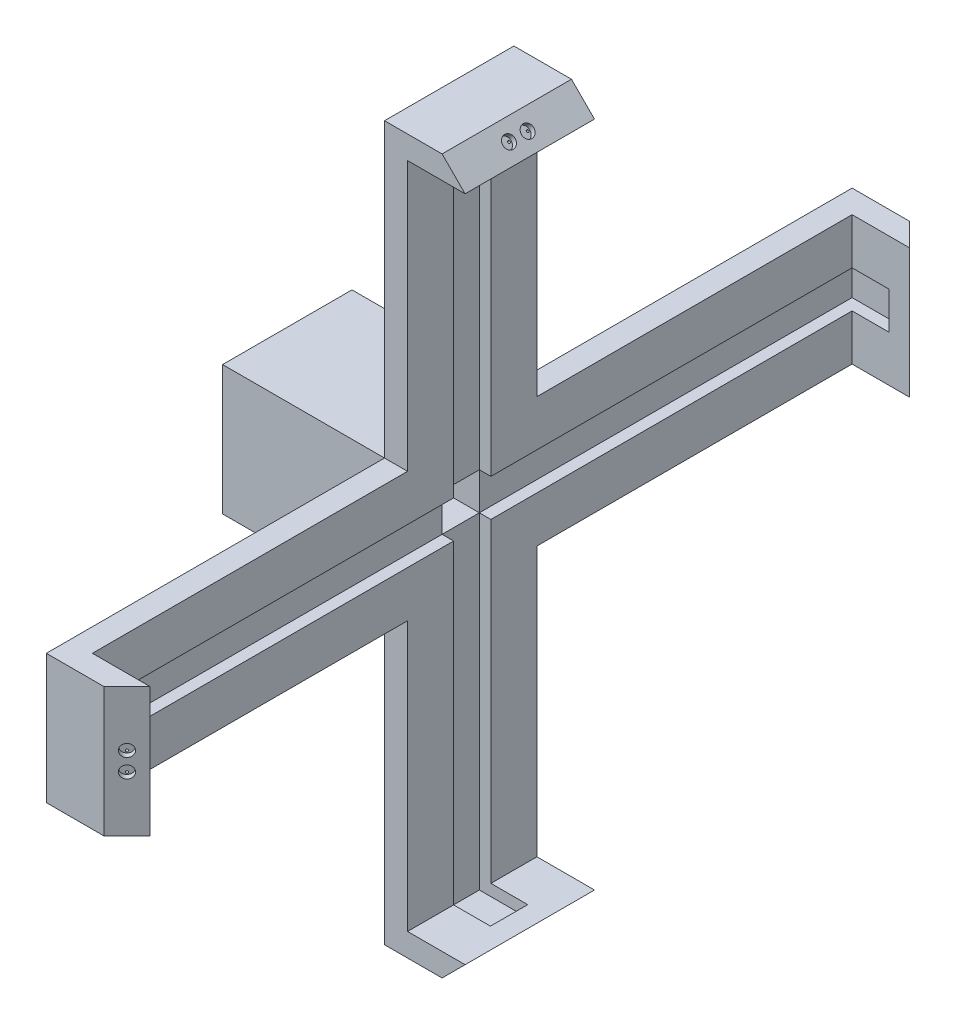
SolidWorks part; units mm, degrees
ref_plane "Front Plane" through (0, 0, 0) normal (0, 0, 1) x (1, 0, 0)
ref_plane "Top Plane" through (0, 0, 0) normal (0, 1, 0) x (1, 0, 0)
ref_plane "Right Plane" through (0, 0, 0) normal (1, 0, 0) x (0, 0, -1)
sketch "Sketch1" plane through (0, 0, 0) normal (0, 0, 1) x (1, 0, 0)
  circle A0 centre (0, 0) radius 28.1
extrude "Boss-Extrude2" add sketch "Sketch1" along normal blind 24
sketch "Sketch3" plane through (0, 0, 0) normal (0, 0, -1) x (-1, 0, 0)
  line L2 (-1.6618, 2.5) -> (1.6618, 2.5)
  arc A1 (-1.6618, 2.5) -> (1.6618, 2.5) centre (0, 0) ccw
extrude "Cut-Extrude2" cut sketch "Sketch3" against normal blind 21.5
sketch "Sketch4" plane through (0, 0, 0) normal (0, 0, -1) x (-1, 0, 0)
  circle A0 centre (0, 0) radius 3
extrude "Cut-Extrude3" cut sketch "Sketch4" against normal blind 9.5
sketch "Sketch6" plane through (0, 0, 0) normal (0, 0, -1) x (-1, 0, 0)
  circle A0 centre (0, 0) radius 6.025
extrude "Cut-Extrude4" cut sketch "Sketch6" against normal blind 6.2
sketch "Sketch7" plane through (0, 0, 24) normal (0, 0, 1) x (1, 0, 0)
  line L1 (-28.1, -28.1) -> (28.1, -28.1)
  line L2 (-28.1, -28.1) -> (-28.1, 28.1)
  line L3 (-28.1, 28.1) -> (28.1, 28.1)
  line L4 (28.1, -28.1) -> (28.1, 28.1)
  line L5 (-28.1, -28.1) -> (28.1, 28.1) construction
  line L6 (-28.1, 28.1) -> (28.1, -28.1) construction
  point P0 (0, 0)
extrude "Boss-Extrude3" add sketch "Sketch7" along normal blind 56.2
sketch "Sketch8" plane through (28.1, 0, 0) normal (1, 0, 0) x (0, 0, -1)
  line L0 (-80.2, 28.1) -> (-24, 28.1) construction
  line L1 (-80.2, 28.1) -> (-24, 28.1)
  line L2 (-80.2, 28.1) -> (-80.2, -28.1)
  line L3 (-80.2, -28.1) -> (-24, -28.1)
  line L4 (-24, 28.1) -> (-24, -28.1)
  line L5 (-80.2, -28.1) -> (-80.2, 28.1) construction
extrude "Boss-Extrude4" add sketch "Sketch8" along normal blind 14.14
sketch "Sketch10" plane through (42.24, 0, 0) normal (1, 0, 0) x (0, 0, -1)
  line L1 (-80.2, 28.1) -> (-24, 28.1)
  line L2 (-80.2, 28.1) -> (-80.2, -28.1)
  line L3 (-80.2, -28.1) -> (-24, -28.1)
  line L4 (-24, 28.1) -> (-24, -28.1)
extrude "Boss-Extrude5" add sketch "Sketch10" along normal blind 10
sketch "Sketch11" plane through (0, 0, 80.2) normal (0, 0, 1) x (1, 0, 0)
  line L1 (52.24, 28.1) -> (-28.1, 28.1) construction
  line L3 (42.24, 28.1) -> (52.24, 28.1)
  line L4 (42.24, 28.1) -> (42.24, -28.1)
  line L5 (42.24, -28.1) -> (52.24, -28.1)
  line L6 (52.24, 28.1) -> (52.24, -28.1)
extrude "Boss-Extrude6" add sketch "Sketch11" along normal blind 146.9
sketch "Sketch12" plane through (0, 28.1, 0) normal (0, 1, 0) x (1, 0, 0)
  line L1 (42.24, -80.2) -> (52.24, -80.2)
  line L2 (42.24, -80.2) -> (42.24, -24)
  line L3 (42.24, -24) -> (52.24, -24)
  line L4 (52.24, -80.2) -> (52.24, -24)
extrude "Boss-Extrude7" add sketch "Sketch12" along normal blind 126.9
sketch "Sketch13" plane through (0, 0, 24) normal (0, 0, -1) x (-1, 0, 0)
  line L1 (-52.24, -28.1) -> (-42.24, -28.1)
  line L2 (-52.24, -28.1) -> (-52.24, 28.1)
  line L3 (-52.24, 28.1) -> (-42.24, 28.1)
  line L4 (-42.24, -28.1) -> (-42.24, 28.1)
extrude "Boss-Extrude8" add sketch "Sketch13" along normal blind 146.9
sketch "Sketch14" plane through (0, -28.1, 0) normal (0, -1, 0) x (-1, 0, 0)
  line L0 (-52.24, -227.1) -> (-52.24, 122.9) construction
  line L1 (-42.24, -24) -> (-52.24, -24)
  line L2 (-42.24, -24) -> (-42.24, -80.2)
  line L3 (-42.24, -80.2) -> (-52.24, -80.2)
  line L4 (-52.24, -24) -> (-52.24, -80.2)
extrude "Boss-Extrude9" add sketch "Sketch14" along normal blind 126.9
sketch "Sketch15" plane through (52.24, 0, 0) normal (1, 0, 0) x (0, 0, -1)
  line L1 (-80.2, 28.1) -> (-227.1, 28.1) construction
  line L3 (-217.1, 28.1) -> (-227.1, 28.1)
  line L4 (-217.1, 28.1) -> (-217.1, -28.1)
  line L5 (-217.1, -28.1) -> (-227.1, -28.1)
  line L6 (-227.1, 28.1) -> (-227.1, -28.1)
extrude "Boss-Extrude10" add sketch "Sketch15" along normal blind 25
sketch "Sketch16" plane through (52.24, 0, 0) normal (1, 0, 0) x (0, 0, -1)
  line L1 (122.9, 28.1) -> (-24, 28.1) construction
  line L3 (112.9, 28.1) -> (122.9, 28.1)
  line L4 (112.9, 28.1) -> (112.9, -28.1)
  line L5 (112.9, -28.1) -> (122.9, -28.1)
  line L6 (122.9, 28.1) -> (122.9, -28.1)
extrude "Boss-Extrude11" add sketch "Sketch16" along normal blind 25
sketch "Sketch17" plane through (52.24, 0, 0) normal (1, 0, 0) x (0, 0, -1)
  line L1 (-80.2, 155) -> (-80.2, 28.1) construction
  line L3 (-80.2, 145) -> (-24, 145)
  line L4 (-80.2, 145) -> (-80.2, 155)
  line L5 (-80.2, 155) -> (-24, 155)
  line L6 (-24, 145) -> (-24, 155)
extrude "Boss-Extrude12" add sketch "Sketch17" along normal blind 25
sketch "Sketch18" plane through (52.24, 0, 0) normal (1, 0, 0) x (0, 0, -1)
  line L1 (-80.2, -155) -> (-80.2, -28.1) construction
  line L3 (-80.2, -145) -> (-24, -145)
  line L4 (-80.2, -145) -> (-80.2, -155)
  line L5 (-80.2, -155) -> (-24, -155)
  line L6 (-24, -145) -> (-24, -155)
extrude "Boss-Extrude13" add sketch "Sketch18" along normal blind 25
sketch "Sketch19" plane through (-28.1, 0, 0) normal (-1, 0, 0) x (0, 0, 1)
  line L7 (26.5, 25.6) -> (77.7, 25.6)
  line L8 (26.5, 25.6) -> (26.5, -25.6)
  line L9 (26.5, -25.6) -> (77.7, -25.6)
  line L10 (77.7, 25.6) -> (77.7, -25.6)
extrude "Cut-Extrude5" cut sketch "Sketch19" against normal blind 63.7
sketch "Sketch20" plane through (0, 0, 0) normal (0, 0, -1) x (-1, 0, 0)
  arc A1 (0, 15) -> (-15, 0) centre (0, 0) ccw
sketch3d "3DSketch2"
  line L2 (0, 15, 0) -> (0, 22.5, 0)
  line L3 (0, 15, 0) -> (0, 15, 42.1431)
  line L4 (0, 15, 42.1431) -> (0, 22.5, 42.1431)
  line L5 (0, 22.5, 0) -> (0, 22.5, 42.1431)
  arc A0 (0, 15, 0) -> (15, 0, 0) centre (0, 0, 0) ccw construction
  point P10 (0, 0, -15)
sweep "Cut-Sweep2" cut profiles "3DSketch2" path "Sketch20"
sketch "Sketch23" plane through (52.24, 0, 0) normal (1, 0, 0) x (0, 0, -1)
  line L1 (-217.1, -28.1) -> (-217.1, 28.1) construction
  line L3 (112.9, 28.1) -> (112.9, -28.1) construction
  line L4 (-217.1, 8.1) -> (112.9, 8.1)
  line L5 (-217.1, 8.1) -> (-217.1, -8.1)
  line L6 (-217.1, -8.1) -> (112.9, -8.1)
  line L7 (112.9, 8.1) -> (112.9, -8.1)
extrude "Cut-Extrude7" cut sketch "Sketch23" against normal blind 5
sketch "Sketch24" plane through (52.24, 0, 0) normal (1, 0, 0) x (0, 0, -1)
  line L1 (-80.2, 145) -> (-24, 145) construction
  line L3 (-24, -145) -> (-80.2, -145) construction
  line L4 (-60.2, 145) -> (-44, 145)
  line L5 (-60.2, 145) -> (-60.2, -145)
  line L6 (-60.2, -145) -> (-44, -145)
  line L7 (-44, 145) -> (-44, -145)
extrude "Cut-Extrude8" cut sketch "Sketch24" against normal blind 5
sketch "Sketch25" plane through (47.24, 0, 0) normal (1, 0, 0) x (0, 0, -1)
  line L1 (-60.2, 8.1) -> (-44, 8.1)
  line L2 (-60.2, 8.1) -> (-60.2, -8.1)
  line L3 (-60.2, -8.1) -> (-44, -8.1)
  line L4 (-44, 8.1) -> (-44, -8.1)
extrude "Cut-Extrude12" cut sketch "Sketch25" against normal blind 25
sketch "Sketch26" plane through (0, -28.1, 0) normal (0, -1, 0) x (-1, 0, 0)
  line L0 (-77.24, -217.1) -> (-67.24, -227.1)
  line L1 (-42.24, -227.1) -> (-77.24, -227.1) construction
  line L2 (-77.24, 112.9) -> (-67.24, 122.9)
  line L3 (-77.24, 112.9) -> (-77.24, 122.9) construction
  line L4 (-77.24, 122.9) -> (-42.24, 122.9) construction
  line L5 (-67.24, -227.1) -> (-77.24, -227.1)
  line L6 (-77.24, -227.1) -> (-77.24, -217.1)
  line L7 (-77.24, 112.9) -> (-77.24, 122.9)
  line L8 (-77.24, 122.9) -> (-67.24, 122.9)
extrude "Cut-Extrude13" cut sketch "Sketch26" against normal blind 56.2
sketch "Sketch27" plane through (0, 0, 80.2) normal (0, 0, 1) x (1, 0, 0)
  line L0 (77.24, -145) -> (67.24, -155)
  line L1 (77.24, -155) -> (42.24, -155) construction
  line L2 (67.24, -155) -> (77.24, -155)
  line L3 (77.24, -155) -> (77.24, -145)
  line L4 (77.24, 145) -> (67.24, 155)
  line L5 (42.24, 155) -> (77.24, 155) construction
  line L6 (77.24, 155) -> (67.24, 155)
  line L7 (77.24, 155) -> (77.24, 145)
extrude "Cut-Extrude14" cut sketch "Sketch27" against normal blind 56.2
sketch "Sketch28" plane through (0, -145, 0) normal (0, 1, 0) x (1, 0, 0)
  line L1 (47.24, -44) -> (68.24, -44)
  line L2 (47.24, -44) -> (47.24, -60.2)
  line L3 (47.24, -60.2) -> (68.24, -60.2)
  line L4 (68.24, -44) -> (68.24, -60.2)
extrude "Cut-Extrude15" cut sketch "Sketch28" against normal blind 5
sketch "Sketch29" plane through (0, 145, 0) normal (0, -1, 0) x (-1, 0, 0)
  line L1 (-47.24, -60.2) -> (-68.24, -60.2)
  line L2 (-47.24, -60.2) -> (-47.24, -44)
  line L3 (-47.24, -44) -> (-68.24, -44)
  line L4 (-68.24, -60.2) -> (-68.24, -44)
extrude "Cut-Extrude16" cut sketch "Sketch29" against normal blind 5
sketch "Sketch30" plane through (0, 0, 217.1) normal (0, 0, -1) x (-1, 0, 0)
  line L1 (-47.24, -8.1) -> (-68.24, -8.1)
  line L2 (-47.24, -8.1) -> (-47.24, 8.1)
  line L3 (-47.24, 8.1) -> (-68.24, 8.1)
  line L4 (-68.24, -8.1) -> (-68.24, 8.1)
extrude "Cut-Extrude17" cut sketch "Sketch30" against normal blind 5
sketch "Sketch31" plane through (0, 0, -112.9) normal (0, 0, 1) x (1, 0, 0)
  line L1 (47.24, 8.1) -> (68.24, 8.1)
  line L2 (47.24, 8.1) -> (47.24, -8.1)
  line L3 (47.24, -8.1) -> (68.24, -8.1)
  line L4 (68.24, 8.1) -> (68.24, -8.1)
extrude "Cut-Extrude18" cut sketch "Sketch31" against normal blind 5
sketch "Sketch33" plane through (147.17, 0, 147.17) normal (0.7071, 0, 0.7071) x (0.7071, 0, -0.7071)
  circle A0 centre (-105.967, 4.05) radius 2.65
  circle A1 centre (-105.967, -4.05) radius 2.65
extrude "Cut-Extrude19" cut sketch "Sketch33" against normal blind 2.4
sketch "Sketch34" plane through (145.4729, 0, 145.4729) normal (0.7071, 0, 0.7071) x (0.7071, 0, -0.7071)
  circle A2 centre (-105.967, 5.75) radius 0.5
  circle A3 centre (-105.967, 2.35) radius 0.5
  circle A4 centre (-105.967, -2.35) radius 0.5
  circle A5 centre (-105.967, -5.75) radius 0.5
extrude "Cut-Extrude20" cut sketch "Sketch34" against normal blind 10
sketch "Sketch35" plane through (95.07, 0, -95.07) normal (0.7071, 0, -0.7071) x (-0.7071, 0, -0.7071)
  circle A0 centre (32.2865, -4.05) radius 2.65
  circle A1 centre (32.2865, 4.05) radius 2.65
extrude "Cut-Extrude21" cut sketch "Sketch35" against normal blind 2.4
sketch "Sketch36" plane through (93.3729, 0, -93.3729) normal (0.7071, 0, -0.7071) x (-0.7071, 0, -0.7071)
  circle A2 centre (32.2865, -5.75) radius 0.5
  circle A3 centre (32.2865, -2.35) radius 0.5
  circle A5 centre (32.2865, 2.35) radius 0.5
  circle A6 centre (32.2865, 5.75) radius 0.5
extrude "Cut-Extrude22" cut sketch "Sketch36" against normal blind 10
sketch "Sketch37" plane through (111.12, -111.12, 0) normal (0.7071, -0.7071, 0) x (0, 0, -1)
  circle A0 centre (-56.15, -54.9846) radius 2.65
  circle A1 centre (-48.05, -54.9846) radius 2.65
extrude "Cut-Extrude23" cut sketch "Sketch37" against normal blind 2.4
sketch "Sketch38" plane through (109.4229, -109.4229, 0) normal (0.7071, -0.7071, 0) x (0, 0, -1)
  circle A2 centre (-57.85, -54.9846) radius 0.5
  circle A3 centre (-54.45, -54.9846) radius 0.5
  circle A4 centre (-49.75, -54.9846) radius 0.5
  circle A5 centre (-46.35, -54.9846) radius 0.5
extrude "Cut-Extrude24" cut sketch "Sketch38" against normal blind 10
sketch "Sketch39" plane through (111.12, 111.12, 0) normal (0.7071, 0.7071, 0) x (0.7071, -0.7071, 0)
  circle A0 centre (-54.9846, -48.05) radius 2.65
  circle A1 centre (-54.9846, -56.15) radius 2.65
extrude "Cut-Extrude25" cut sketch "Sketch39" against normal blind 2.4
sketch "Sketch40" plane through (109.4229, 109.4229, 0) normal (0.7071, 0.7071, 0) x (0.7071, -0.7071, 0)
  circle A2 centre (-54.9846, -46.35) radius 0.5
  circle A3 centre (-54.9846, -49.75) radius 0.5
  circle A4 centre (-54.9846, -54.45) radius 0.5
  circle A5 centre (-54.9846, -57.85) radius 0.5
extrude "Cut-Extrude26" cut sketch "Sketch40" against normal blind 10
sketch "Sketch41" plane through (0, 0, 0) normal (0, 0, -1) x (-1, 0, 0)
  circle A0 centre (0, 18.75) radius 3.75
  circle A1 centre (-18.75, 0) radius 3.75
extrude "Cut-Extrude28" cut sketch "Sketch41" against normal blind 30
